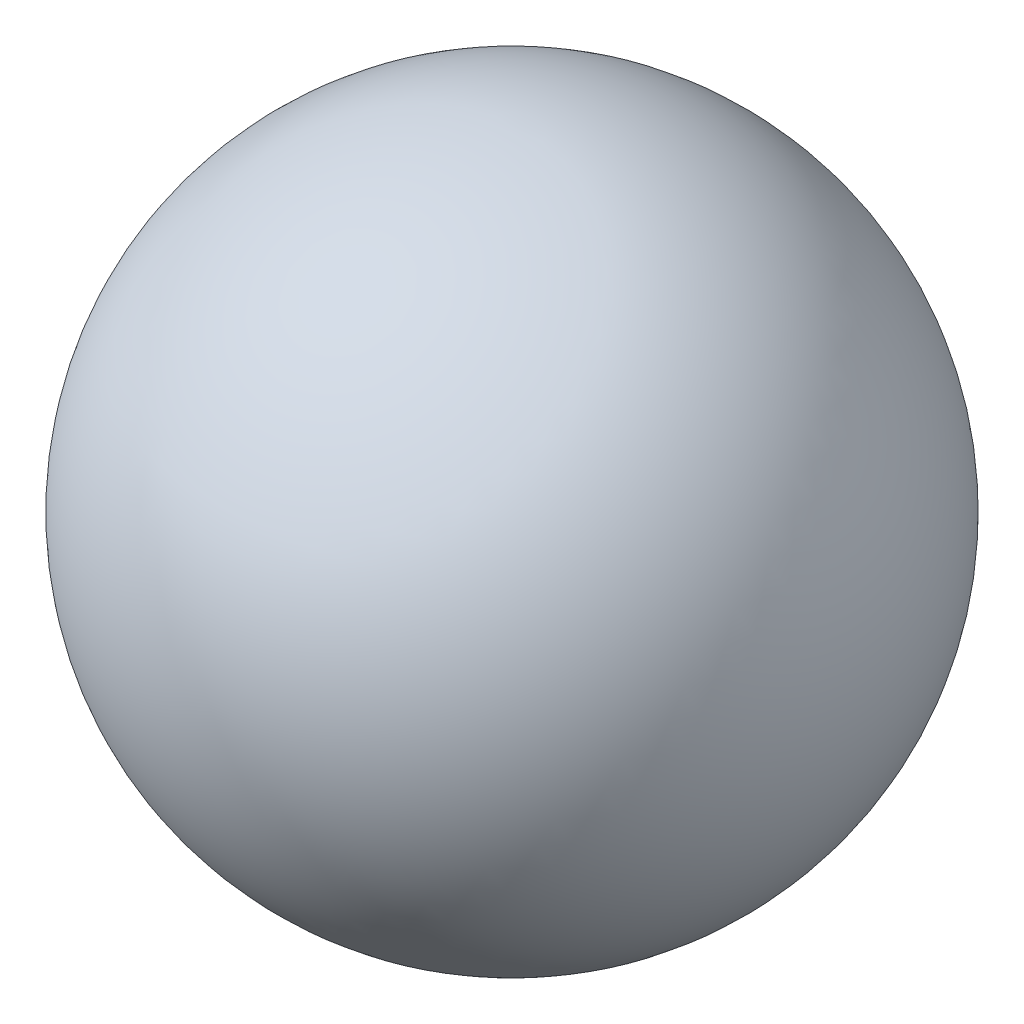
SolidWorks part; units mm, degrees
ref_plane "Front Plane" through (0, 0, 0) normal (0, 0, 1) x (1, 0, 0)
ref_plane "Top Plane" through (0, 0, 0) normal (0, 1, 0) x (1, 0, 0)
ref_plane "Right Plane" through (0, 0, 0) normal (1, 0, 0) x (0, 0, -1)
sketch "Sketch2" plane through (0, 0, 0) normal (0, 0, 1) x (1, 0, 0)
  line L0 (0, -158.4863) -> (0, 158.4863) construction
  line L1 (0, 12.7) -> (0, 12.2174)
  line L2 (0, -12.2174) -> (0, -12.7)
  arc A0 (0, -12.7) -> (0, 12.7) centre (0, 0) ccw
  arc A1 (0, -12.2174) -> (0, 12.2174) centre (0, 0) ccw
  circle A2 centre (0, 0) radius 12.7 construction
  circle A3 centre (0, 0) radius 12.2174 construction
  point P4 (0, 0)
  dimension "D2" = 12.7
  dimension "D1" = 0.4826
revolve "Revolve1" add sketch "Sketch2" angle 360 about L0
